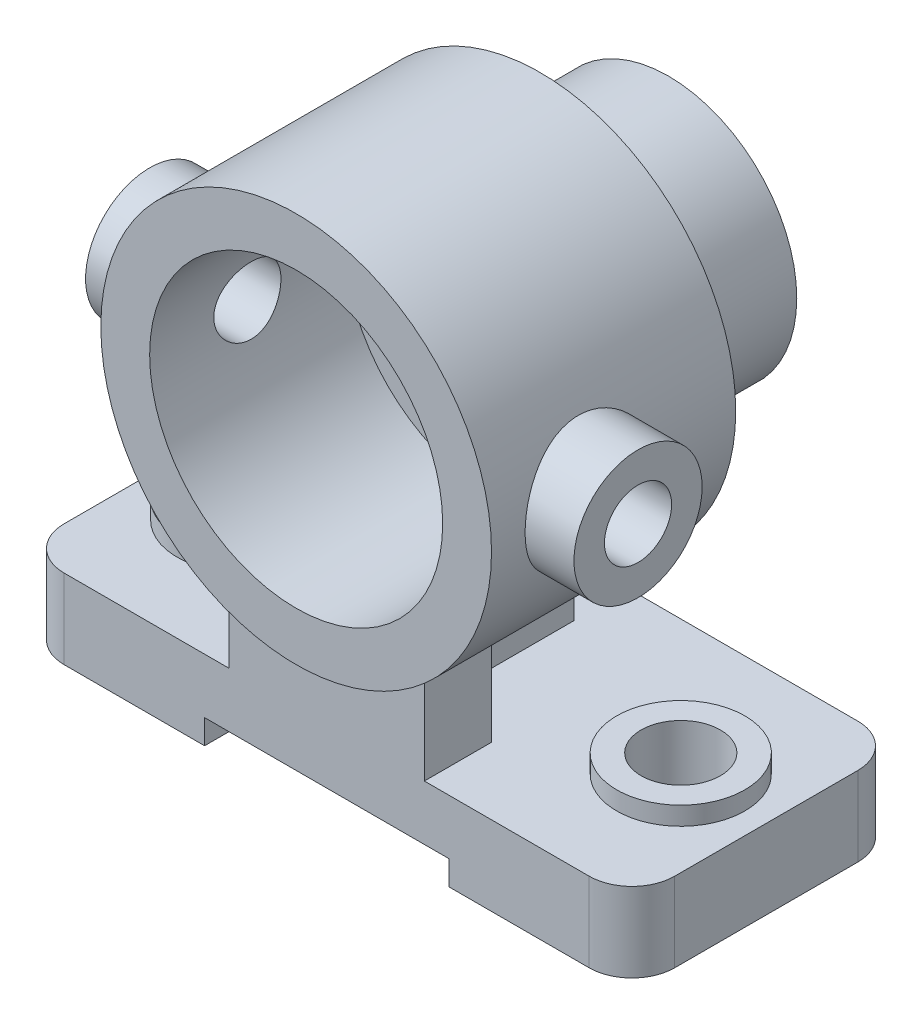
SolidWorks part; units mm, degrees
ref_plane "前视基准面" through (0, 0, 0) normal (0, 0, 1) x (1, 0, 0)
ref_plane "上视基准面" through (0, 0, 0) normal (0, 1, 0) x (1, 0, 0)
ref_plane "右视基准面" through (0, 0, 0) normal (1, 0, 0) x (0, 0, -1)
sketch "草图1" plane through (0, 0, 0) normal (0, 1, 0) x (1, 0, 0)
  line L1 (-43, -22) -> (43, -22)
  line L2 (-50, -15) -> (-50, 15)
  line L3 (-43, 22) -> (43, 22)
  line L4 (50, -15) -> (50, 15)
  line L5 (-50, -22) -> (50, 22) construction
  line L6 (-50, 22) -> (50, -22) construction
  arc A0 (-50, 15) -> (-43, 22) centre (-43, 15) cw
  arc A1 (-43, -22) -> (-50, -15) centre (-43, -15) cw
  arc A2 (50, -15) -> (43, -22) centre (43, -15) cw
  arc A3 (43, 22) -> (50, 15) centre (43, 15) cw
  point P0 (0, 0)
  dimension "D3" = 7
  dimension "D4" = 7
  dimension "D5" = 7
  dimension "D6" = 7
  dimension "D1" = 100
  dimension "D2" = 44
extrude "凸台-拉伸1" add sketch "草图1" along normal blind 13
sketch "草图2" plane through (0, 13, 0) normal (0, 1, 0) x (1, 0, 0)
  line L0 (-7.15, 0) -> (7.15, 0) construction
  line L1 (0, -7.15) -> (0, 7.15) construction
  circle A0 centre (-36, 0) radius 10.5
  circle A1 centre (36, 0) radius 10.5
  dimension "D1" = 36
  dimension "D2" = 21
extrude "凸台-拉伸2" add sketch "草图2" along normal blind 3
sketch "草图3" plane through (0, 13, 0) normal (0, 1, 0) x (1, 0, 0)
  line L0 (-43, -22) -> (43, -22) construction
  line L1 (16, -22) -> (-16, -22)
  line L2 (16, -22) -> (16, -11)
  line L3 (16, -11) -> (5.5, -11)
  line L4 (-16, -22) -> (-16, -11)
  line L5 (0, -8.8) -> (0, 8.8) construction
  line L6 (-5.5, -11) -> (-16, -11)
  line L8 (5.5, -11) -> (5.5, 13)
  line L9 (5.5, 13) -> (-5.5, 13)
  line L10 (-5.5, -11) -> (-5.5, 13)
  dimension "D1" = 32
  dimension "D2" = 16
  dimension "D3" = 11
  dimension "D4" = 11
  dimension "D5" = 5.5
  dimension "D6" = 35
extrude "凸台-拉伸3" add sketch "草图3" along normal blind 56
sketch "草图4" plane through (0, 0, 22) normal (0, 0, 1) x (1, 0, 0)
  line L0 (0, -24.2) -> (0, 24.2) construction
  line L1 (24.2, 0) -> (-24.2, 0) construction
  circle A0 centre (0, 56) radius 32
  dimension "D1" = 64
  dimension "D2" = 56
extrude "凸台-拉伸4" add sketch "草图4" along normal blind 5 and the other way blind 35
sketch "草图5" plane through (0, 0, -13) normal (0, 0, -1) x (-1, 0, 0)
  line L0 (0, 26.95) -> (0, -26.95) construction
  circle A0 centre (0, 56) radius 21
  arc A1 (5.5, 24.4762) -> (-5.5, 24.4762) centre (0, 56) ccw construction
  dimension "D1" = 42
extrude "凸台-拉伸5" add sketch "草图5" along normal blind 21
sketch "草图6" plane through (0, 0, 0) normal (1, 0, 0) x (0, 0, -1)
  line L0 (33.55, 0) -> (-33.55, 0) construction
  line L1 (-27, 88) -> (-27, 24) construction
  circle A0 centre (-11, 56) radius 10.5
  dimension "D1" = 21
  dimension "D2" = 56
  dimension "D3" = 16
extrude "凸台-拉伸6" add sketch "草图6" along normal blind 40
mirror "镜向1" about plane through (0, 0, 0) normal (1, 0, 0) of "凸台-拉伸6"
sketch "草图7" plane through (-40, 0, 0) normal (-1, 0, 0) x (0, 0, 1)
  circle A0 centre (11, 56) radius 5.5
  circle A1 centre (11, 56) radius 10.5 construction
  point P2 (0, 0)
  dimension "D1" = 11
extrude "切除-拉伸1" cut sketch "草图7" against normal through all
sketch "草图8" plane through (0, 0, 27) normal (0, 0, 1) x (1, 0, 0)
  circle A0 centre (0, 56) radius 24
  dimension "D1" = 48
extrude "切除-拉伸2" cut sketch "草图8" against normal blind 32
sketch "草图9" plane through (0, 0, -5) normal (0, 0, 1) x (1, 0, 0)
  circle A0 centre (0, 56) radius 12
  dimension "D1" = 24
extrude "切除-拉伸3" cut sketch "草图9" against normal blind 21
sketch "草图10" plane through (0, 16, 0) normal (0, 1, 0) x (1, 0, 0)
  line L0 (0, -33.55) -> (0, 33.55) construction
  circle A0 centre (-36, 0) radius 6.5
  circle A1 centre (36, 0) radius 6.5
extrude "切除-拉伸4" cut sketch "草图10" against normal through all
sketch "草图11" plane through (0, 0, 22) normal (0, 0, 1) x (1, 0, 0)
  line L1 (-20, -4) -> (20, -4)
  line L2 (-20, -4) -> (-20, 4)
  line L3 (-20, 4) -> (20, 4)
  line L4 (20, -4) -> (20, 4)
  line L5 (-20, -4) -> (20, 4) construction
  line L6 (-20, 4) -> (20, -4) construction
  point P0 (0, 0)
  dimension "D1" = 40
  dimension "D2" = 8
extrude "切除-拉伸5" cut sketch "草图11" against normal through all
